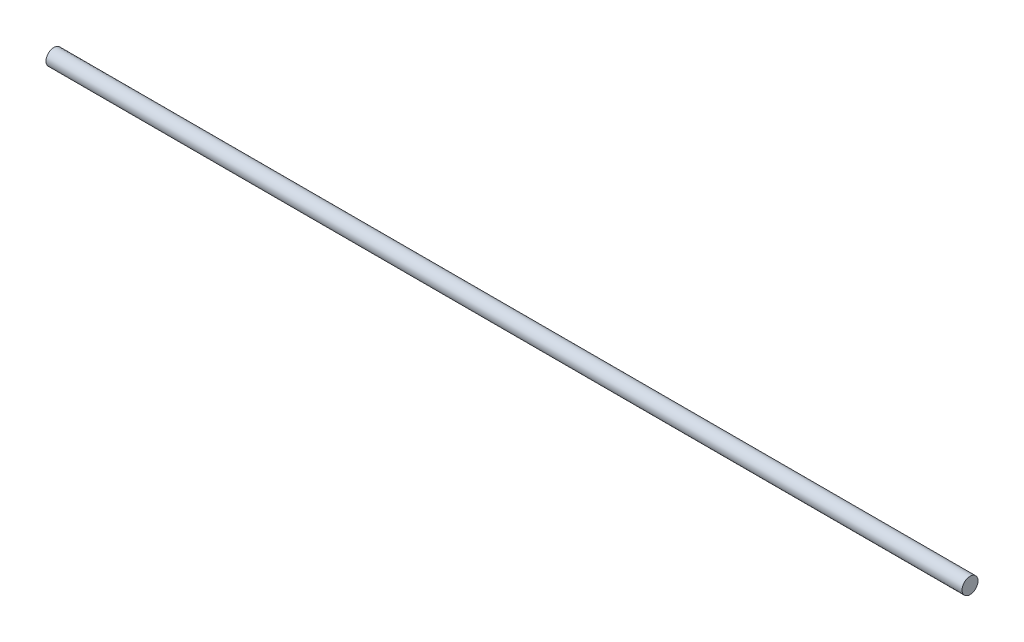
SolidWorks part; units mm, degrees
ref_plane "Front Plane" through (0, 0, 0) normal (0, 0, 1) x (1, 0, 0)
ref_plane "Top Plane" through (0, 0, 0) normal (0, 1, 0) x (1, 0, 0)
ref_plane "Right Plane" through (0, 0, 0) normal (1, 0, 0) x (0, 0, -1)
sketch "Sketch1" plane through (0, 0, 0) normal (1, 0, 0) x (0, 0, -1)
  circle A0 centre (0, 0) radius 4
  dimension "D1" = 8
extrude "Boss-Extrude1" add sketch "Sketch1" along normal blind 460 contours A0
